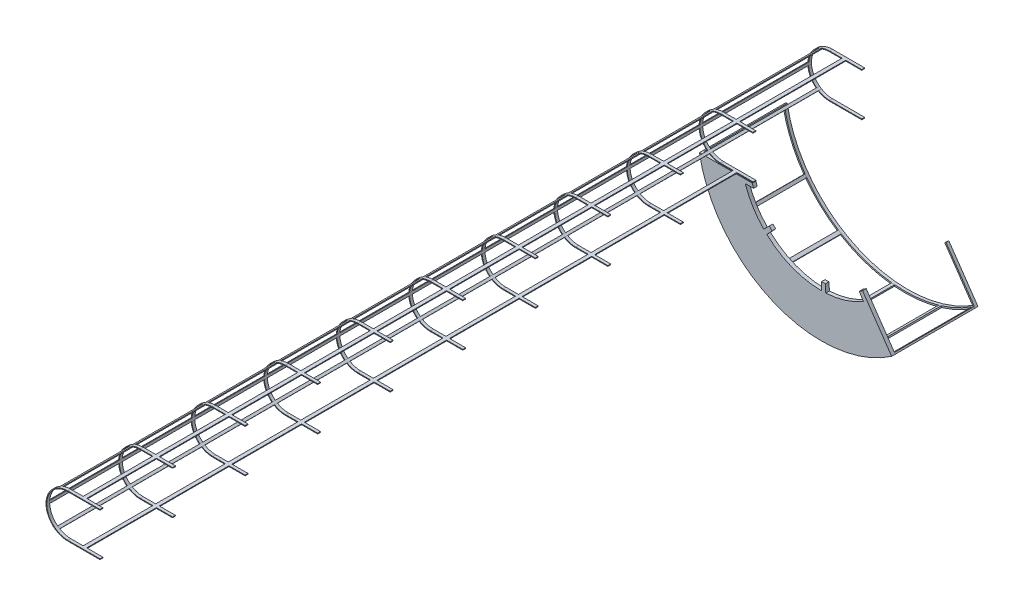
SolidWorks part; units mm, degrees
ref_plane "Front Plane" through (0, 0, 0) normal (0, 0, 1) x (1, 0, 0)
ref_plane "Top Plane" through (0, 0, 0) normal (0, 1, 0) x (1, 0, 0)
ref_plane "Right Plane" through (0, 0, 0) normal (1, 0, 0) x (0, 0, -1)
sketch "Sketch2" plane through (0, 0, 0) normal (0, 0, 1) x (1, 0, 0)
  line L10 (1635.833, 3341.4613) -> (908.3583, 3341.4613)
  line L11 (1654.5071, 3287.5133) -> (1635.833, 3341.4613)
  line L12 (1539.8615, 3287.5133) -> (1654.5071, 3287.5133)
  line L13 (1871.36, 2945.8437) -> (1793.795, 2870.7396)
  line L14 (1836.6838, 2828.7808) -> (1910.0696, 2907.9736)
  line L15 (2589.7722, 2641.4613) -> (2589.7722, 2533.494)
  line L16 (2649.7722, 2535.1197) -> (2643.9254, 2642.9287)
  line L17 (3111.0925, 2788.1003) -> (3167.3781, 2695.9651)
  line L18 (3217.7141, 2728.6192) -> (3156.5234, 2817.5723)
  line L19 (3557.7648, 2234.2858) -> (3217.7141, 2728.6192)
  line L20 (1635.833, 3341.4613) -> (908.3583, 3341.4613)
  line L21 (1654.5071, 3287.5133) -> (1635.833, 3341.4613)
  line L22 (1539.8615, 3287.5133) -> (1654.5071, 3287.5133)
  line L23 (1871.36, 2945.8437) -> (1793.795, 2870.7396)
  line L24 (1836.6838, 2828.7808) -> (1910.0696, 2907.9736)
  line L25 (2589.7722, 2641.4613) -> (2589.7722, 2533.494)
  line L26 (2649.7722, 2535.1197) -> (2643.9254, 2642.9287)
  line L27 (3111.0925, 2788.1003) -> (3167.3781, 2695.9651)
  line L28 (3217.7141, 2728.6192) -> (3156.5234, 2817.5723)
  line L29 (3557.7648, 2234.2858) -> (3217.7141, 2728.6192)
  arc A7 (1539.8615, 3287.5133) -> (1793.795, 2870.7396) centre (2589.7722, 3641.4613) ccw
  arc A8 (1871.36, 2945.8437) -> (1910.0696, 2907.9736) centre (2589.7722, 3641.4613) ccw
  arc A9 (1836.6838, 2828.7808) -> (2589.7722, 2533.494) centre (2589.7722, 3641.4613) ccw
  arc A10 (2589.7722, 2641.4613) -> (2643.9254, 2642.9287) centre (2589.7722, 3641.4613) ccw
  arc A11 (2649.7722, 2535.1197) -> (3167.3781, 2695.9651) centre (2589.7722, 3641.4613) ccw
  arc A12 (3111.0925, 2788.1003) -> (3156.5234, 2817.5723) centre (2589.7722, 3641.4613) ccw
  arc A13 (908.3583, 3341.4613) -> (3557.7648, 2234.2858) centre (2589.7722, 3641.4613) ccw
  arc A14 (1539.8615, 3287.5133) -> (1793.795, 2870.7396) centre (2589.7722, 3641.4613) ccw
  arc A15 (1871.36, 2945.8437) -> (1910.0696, 2907.9736) centre (2589.7722, 3641.4613) ccw
  arc A16 (1836.6838, 2828.7808) -> (2589.7722, 2533.494) centre (2589.7722, 3641.4613) ccw
  arc A17 (2589.7722, 2641.4613) -> (2643.9254, 2642.9287) centre (2589.7722, 3641.4613) ccw
  arc A18 (2649.7722, 2535.1197) -> (3167.3781, 2695.9651) centre (2589.7722, 3641.4613) ccw
  arc A19 (3111.0925, 2788.1003) -> (3156.5234, 2817.5723) centre (2589.7722, 3641.4613) ccw
  arc A20 (908.3583, 3341.4613) -> (3557.7648, 2234.2858) centre (2589.7722, 3641.4613) ccw
  dimension "D1" = 0
extrude "Extrude1" add sketch "Sketch2" along normal blind 50
sketch "Sketch3" plane through (0, 0, 0) normal (0, 0, -1) x (-1, 0, 0)
  line L0 (-2589.7722, 3641.4613) -> (-572.38, 3641.4613) construction
  line L1 (-1635.833, 3341.4613) -> (-1192.3316, 3341.4613)
  line L2 (-1635.833, 3341.4613) -> (-908.3583, 3341.4613) construction
  line L3 (-1635.833, 3941.4613) -> (-1192.3316, 3941.4613)
  line L4 (-1635.833, 3351.4613) -> (-1192.3316, 3351.4613)
  line L5 (-1635.833, 3931.4613) -> (-1192.3316, 3931.4613)
  line L6 (-1635.833, 3941.4613) -> (-1635.833, 3931.4613)
  line L7 (-1635.833, 3341.4613) -> (-1635.833, 3351.4613)
  arc A0 (-1192.3316, 3341.4613) -> (-1192.3316, 3941.4613) centre (-1192.3316, 3641.4613) ccw
  arc A1 (-1192.3316, 3351.4613) -> (-1192.3316, 3931.4613) centre (-1192.3316, 3641.4613) ccw
  dimension "D1" = 600
  dimension "D2" = 10
extrude "Extrude2" add sketch "Sketch3" against normal blind 40
sketch "Sketch4" plane through (0, 0, 0) normal (0, 0, -1) x (-1, 0, 0)
  line L0 (-1414.0823, 3941.4613) -> (-1364.1957, 3941.4613)
  line L1 (-1414.0823, 3941.4613) -> (-1414.0823, 3931.4613)
  line L2 (-1364.1957, 3941.4613) -> (-1364.1957, 3931.4613)
  line L3 (-1414.0823, 3931.4613) -> (-1364.1957, 3931.4613)
  line L4 (-1192.3316, 3941.4613) -> (-1635.833, 3941.4613) construction
  line L5 (-1635.833, 3931.4613) -> (-1192.3316, 3931.4613) construction
  line L6 (-1084.8859, 3921.5603) -> (-1051.6395, 3906.425)
  line L7 (-1084.8859, 3921.5603) -> (-1089.0372, 3912.4415)
  line L8 (-1051.6395, 3906.425) -> (-1055.7908, 3897.3062)
  line L9 (-1089.0372, 3912.4415) -> (-1055.7908, 3897.3062)
  line L10 (-893.1493, 3663.5962) -> (-892.8174, 3624.3966)
  line L11 (-893.1493, 3663.5962) -> (-903.1711, 3663.5113)
  line L12 (-892.8174, 3624.3966) -> (-902.8391, 3624.3117)
  line L13 (-903.1711, 3663.5113) -> (-902.8391, 3624.3117)
  line L14 (-1013.3886, 3413.2522) -> (-1041.563, 3393.734)
  line L15 (-1013.3886, 3413.2522) -> (-1007.6843, 3405.0181)
  line L16 (-1041.563, 3393.734) -> (-1035.8587, 3385.4999)
  line L17 (-1007.6843, 3405.0181) -> (-1035.8587, 3385.4999)
  line L18 (-1414.0823, 3351.4613) -> (-1414.0823, 3341.4613)
  line L19 (-1414.0823, 3351.4613) -> (-1364.1957, 3351.4613)
  line L20 (-1414.0823, 3341.4613) -> (-1364.1957, 3341.4613)
  line L21 (-1364.1957, 3351.4613) -> (-1364.1957, 3341.4613)
  line L23 (-1192.3316, 3351.4613) -> (-1635.833, 3351.4613) construction
  arc A0 (-1192.3316, 3341.4613) -> (-1192.3316, 3941.4613) centre (-1192.3316, 3641.4613) ccw construction
  arc A1 (-1192.3316, 3351.4613) -> (-1192.3316, 3931.4613) centre (-1192.3316, 3641.4613) ccw construction
extrude "Extrude3" add sketch "Sketch4" against normal blind 9000 and the other way blind 1500
pattern_linear "LPattern1" count 9 spacing 1000 along (0, 0, 1) of "Extrude2"
pattern_linear "LPattern2" count 2 spacing 1500 along (0, 0, -1) of "Extrude2"
sketch "Sketch5" plane through (0, 3341.4613, 0) normal (0, -1, 0) x (1, 0, 0)
  line L1 (1414.0823, -1460) -> (1359.5524, -1460)
  line L2 (1414.0823, -1460) -> (1414.0823, 0)
  line L3 (1414.0823, 0) -> (1359.5524, 0)
  line L4 (1359.5524, -1460) -> (1359.5524, 0)
extrude "Cut-Extrude1" cut sketch "Sketch5" against normal up to next
sketch "Sketch6" plane through (0, 0, 0) normal (0, 0, -1) x (-1, 0, 0)
  line L0 (-908.3583, 3341.4613) -> (-915.9883, 3301.4613)
  line L1 (-908.3583, 3341.4613) -> (-928.0041, 3345.2087)
  line L2 (-915.9883, 3301.4613) -> (-935.6341, 3305.2087)
  line L3 (-928.0041, 3345.2087) -> (-935.6341, 3305.2087)
  line L4 (-1197.4988, 2652.1548) -> (-1221.0483, 2619.8218)
  line L5 (-1197.4988, 2652.1548) -> (-1213.6654, 2663.9295)
  line L6 (-1221.0483, 2619.8218) -> (-1237.2148, 2631.5965)
  line L7 (-1213.6654, 2663.9295) -> (-1237.2148, 2631.5965)
  line L8 (-1662.0171, 2207.4379) -> (-1702.0171, 2182.3371)
  line L9 (-1662.0171, 2207.4379) -> (-1672.6478, 2224.3787)
  line L10 (-1702.0171, 2182.3371) -> (-1712.6478, 2199.2778)
  line L11 (-1672.6478, 2224.3787) -> (-1712.6478, 2199.2778)
  line L12 (-2406.2838, 1943.3787) -> (-2446.0999, 1939.5475)
  line L13 (-2406.2838, 1943.3787) -> (-2408.1995, 1963.2868)
  line L14 (-2446.0999, 1939.5475) -> (-2448.0156, 1959.4555)
  line L15 (-2408.1995, 1963.2868) -> (-2448.0156, 1959.4555)
  line L16 (-3058.894, 1999.1832) -> (-3097.2243, 2010.6195)
  line L17 (-3058.894, 1999.1832) -> (-3053.1758, 2018.3484)
  line L18 (-3097.2243, 2010.6195) -> (-3091.5061, 2029.7847)
  line L19 (-3053.1758, 2018.3484) -> (-3091.5061, 2029.7847)
  line L20 (-3557.7648, 2234.2858) -> (-3524.546, 2212.0032)
  line L21 (-3557.7648, 2234.2858) -> (-3546.6235, 2250.8952)
  line L22 (-3524.546, 2212.0032) -> (-3513.4047, 2228.6126)
  line L23 (-3546.6235, 2250.8952) -> (-3513.4047, 2228.6126)
  arc A0 (-3557.7648, 2234.2858) -> (-908.3583, 3341.4613) centre (-2589.7722, 3641.4613) ccw construction
  dimension "D1" = 40
  dimension "D2" = 20
  dimension "D3" = 40
  dimension "D4" = 20
  dimension "D5" = 40
  dimension "D6" = 20
  dimension "D7" = 40
  dimension "D8" = 20
  dimension "D9" = 40
  dimension "D10" = 20
  dimension "D11" = 20
  dimension "D12" = 40
extrude "Extrude4" add sketch "Sketch6" along normal blind 1100
sketch "Sketch7" plane through (0, 0, -1100) normal (0, 0, -1) x (-1, 0, 0)
  line L0 (-3557.7648, 2234.2858) -> (-3156.5234, 2817.5723) construction
  line L1 (-3557.7648, 2234.2858) -> (-3156.5234, 2817.5723)
  line L2 (-3529.8848, 2239.5262) -> (-3140.0456, 2806.2373)
  line L3 (-3156.5234, 2817.5723) -> (-3140.0456, 2806.2373)
  line L4 (-928.0474, 3344.9743) -> (-908.3583, 3341.4613)
  line L5 (-908.3583, 3341.4613) -> (-908.4213, 3342.2941)
  arc A0 (-3557.7648, 2234.2858) -> (-908.3583, 3341.4613) centre (-2589.7722, 3641.4613) ccw construction
  arc A1 (-3557.7648, 2234.2858) -> (-908.3583, 3341.4613) centre (-2589.7722, 3641.4613) ccw
  arc A2 (-3529.8848, 2239.5262) -> (-928.0474, 3344.9743) centre (-2589.7722, 3641.4613) ccw
  dimension "D1" = 20
extrude "Extrude5" add sketch "Sketch7" along normal blind 40 contours A1 L1 L3 L2 A2 L4
pattern_linear "LPattern3" count 2 spacing 9000 along (0, 0, 1) of "Extrude2"
